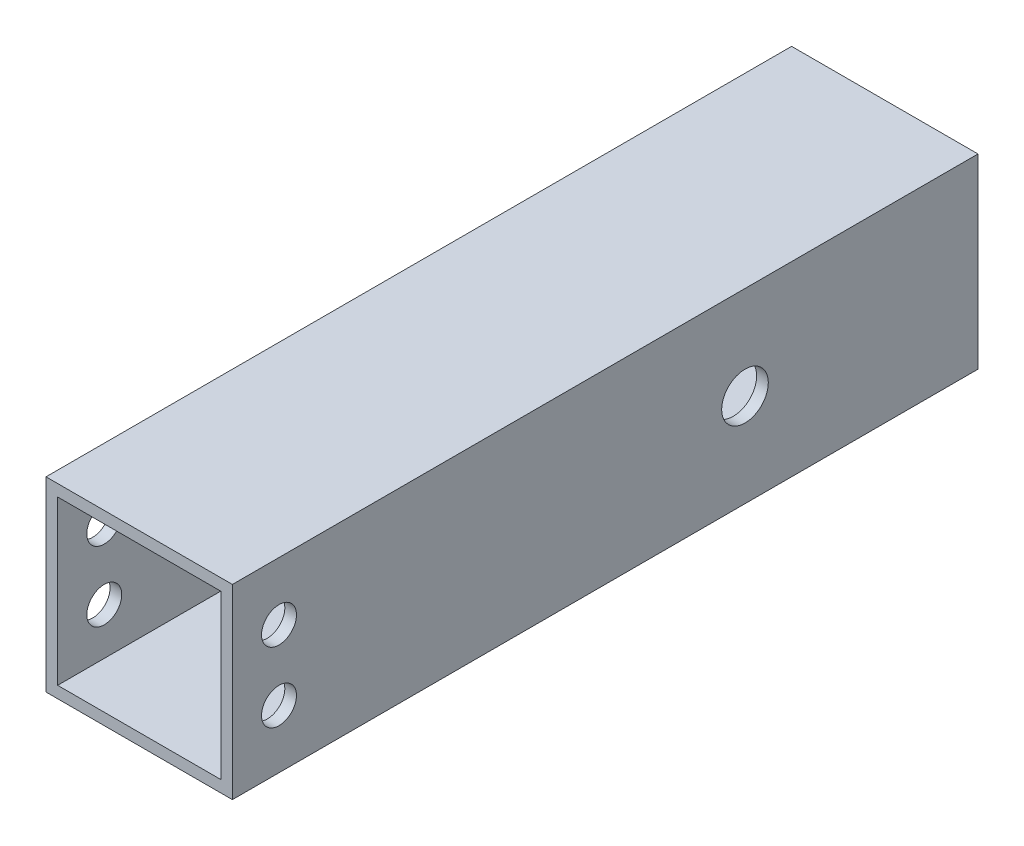
SolidWorks part; units mm, degrees
material "6061-T6 (SS)"
ref_plane "Front Plane" through (0, 0, 0) normal (0, 0, 1) x (1, 0, 0)
ref_plane "Top Plane" through (0, 0, 0) normal (0, 1, 0) x (1, 0, 0)
ref_plane "Right Plane" through (0, 0, 0) normal (1, 0, 0) x (0, 0, -1)
sketch "Sketch1" plane through (0, 0, 0) normal (0, 0, 1) x (1, 0, 0)
  line L1 (-11.1125, -11.1125) -> (11.1125, -11.1125)
  line L2 (-11.1125, -11.1125) -> (-11.1125, 11.1125)
  line L3 (-11.1125, 11.1125) -> (11.1125, 11.1125)
  line L4 (11.1125, -11.1125) -> (11.1125, 11.1125)
  line L5 (-11.1125, -11.1125) -> (11.1125, 11.1125) construction
  line L6 (-11.1125, 11.1125) -> (11.1125, -11.1125) construction
  line L7 (-12.7, -12.7) -> (12.7, -12.7)
  line L8 (-12.7, -12.7) -> (-12.7, 12.7)
  line L9 (-12.7, 12.7) -> (12.7, 12.7)
  line L10 (12.7, -12.7) -> (12.7, 12.7)
  line L11 (-12.7, -12.7) -> (12.7, 12.7) construction
  line L12 (-12.7, 12.7) -> (12.7, -12.7) construction
  point P0 (0, 0)
  point P6 (0, 0)
  dimension "D1" = 25.4
  dimension "D2" = 25.4
  dimension "D3" = 1.5875
  dimension "D4" = 1.5875
extrude "Boss-Extrude1" add sketch "Sketch1" along normal blind 101.6
sketch "Sketch2" plane through (12.7, 0, 0) normal (1, 0, 0) x (0, 0, -1)
  line L0 (-95.25, -4.7625) -> (-95.25, 4.7625) construction
  line L1 (0, -12.7) -> (0, 12.7) construction
  line L2 (-101.6, -12.7) -> (-101.6, 12.7) construction
  circle A0 centre (-95.25, 4.7625) radius 2.3813
  circle A1 centre (-95.25, -4.7625) radius 2.3813
  circle A2 centre (-31.75, 0) radius 3.175
  point P6 (-95.25, 0)
  dimension "D1" = 6.35
  dimension "D2" = 4.7625
  dimension "D3" = 4.7625
  dimension "D4" = 9.525
  dimension "D5" = 31.75
  dimension "D6" = 6.35
extrude "Cut-Extrude1" cut sketch "Sketch2" against normal up to surface (25.4 mm away) up to face at (-12.7, 0, 50.8)
